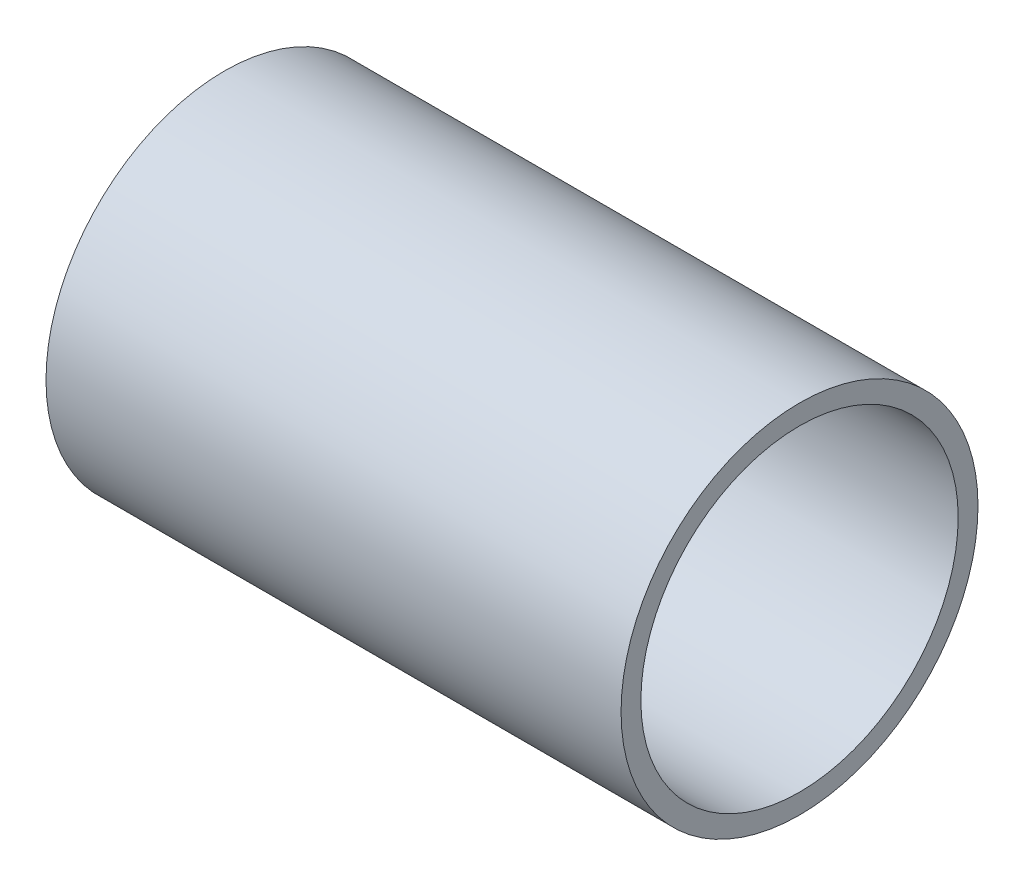
SolidWorks part; units mm, degrees
ref_plane "Front Plane" through (0, 0, 0) normal (0, 0, 1) x (1, 0, 0)
ref_plane "Top Plane" through (0, 0, 0) normal (0, 1, 0) x (1, 0, 0)
ref_plane "Right Plane" through (0, 0, 0) normal (1, 0, 0) x (0, 0, -1)
sketch "Sketch1" plane through (0, 0, 0) normal (1, 0, 0) x (0, 0, -1)
  circle A0 centre (0, 0) radius 45
  circle A1 centre (0, 0) radius 40
  dimension "D1" = 90
  dimension "D2" = 80
extrude "Boss-Extrude1" add sketch "Sketch1" along normal blind 145
